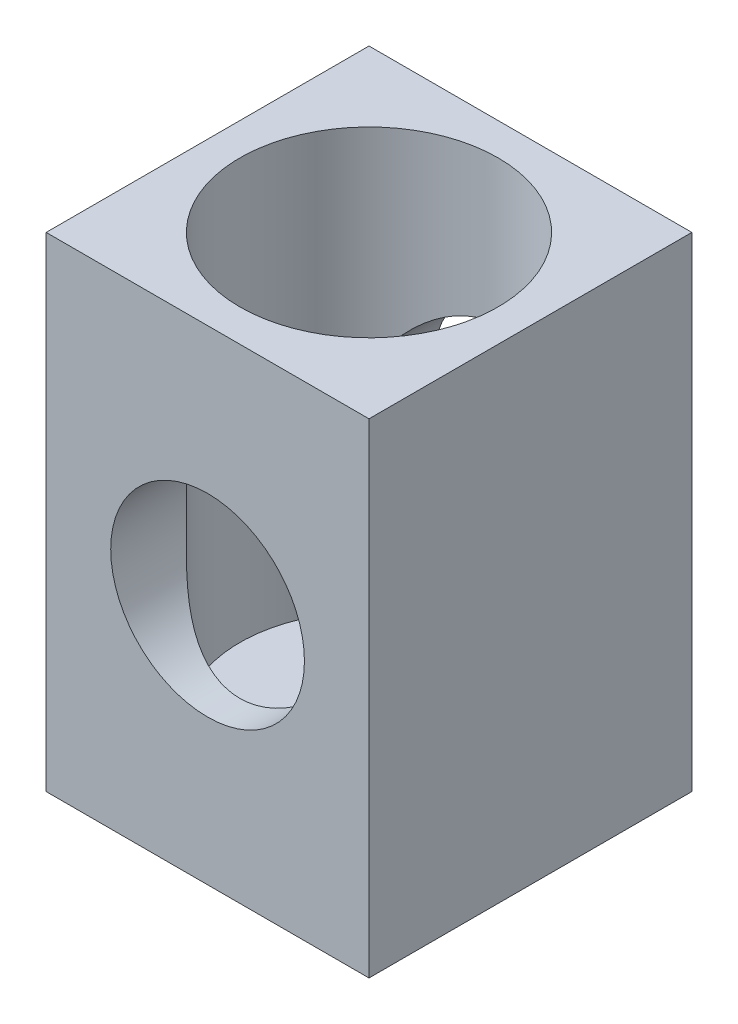
SolidWorks part; units mm, degrees
ref_plane "Front Plane" through (0, 0, 0) normal (0, 0, 1) x (1, 0, 0)
ref_plane "Top Plane" through (0, 0, 0) normal (0, 1, 0) x (1, 0, 0)
ref_plane "Right Plane" through (0, 0, 0) normal (1, 0, 0) x (0, 0, -1)
sketch "Sketch1" plane through (0, 0, 0) normal (0, 0, 1) x (1, 0, 0)
  line L1 (-5, -7.5) -> (5, -7.5)
  line L2 (-5, -7.5) -> (-5, 7.5)
  line L3 (-5, 7.5) -> (5, 7.5)
  line L4 (5, -7.5) -> (5, 7.5)
  line L5 (-5, -7.5) -> (5, 7.5) construction
  line L6 (-5, 7.5) -> (5, -7.5) construction
  circle A0 centre (0, 0) radius 3
  point P0 (0, 0)
  dimension "D1" = 15
  dimension "thickness" = 10
extrude "Boss-Extrude1" add sketch "Sketch1" along normal blind 10
sketch "Sketch3" plane through (0, 7.5, 0) normal (0, 1, 0) x (1, 0, 0)
  line L0 (0, 0) -> (0, -10) construction
  line L1 (5, -10) -> (-5, -10) construction
  line L2 (-5, -5) -> (5, -5) construction
  line L3 (-5, -10) -> (-5, 0) construction
  line L4 (5, -10) -> (5, 0) construction
  circle A0 centre (0, -5) radius 4
extrude "Cut-Extrude1" cut sketch "Sketch3" against normal blind 13
